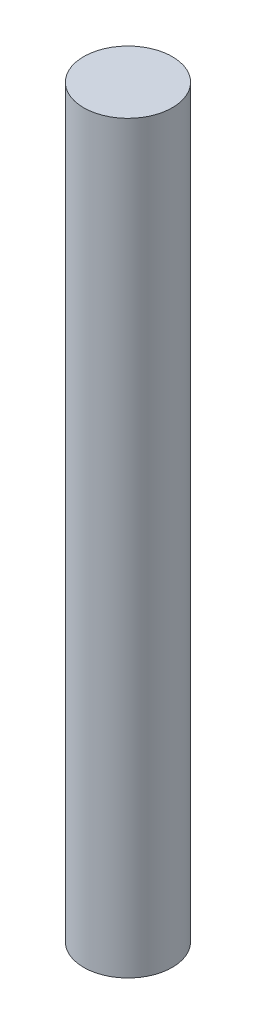
SolidWorks part; units mm, degrees
ref_plane "Front" through (0, 0, 0) normal (0, 0, 1) x (1, 0, 0)
ref_plane "Top" through (0, 0, 0) normal (0, 1, 0) x (1, 0, 0)
ref_plane "Right" through (0, 0, 0) normal (1, 0, 0) x (0, 0, -1)
sketch "Sketch1" plane through (0, 0, 0) normal (0, 1, 0) x (1, 0, 0)
  circle A0 centre (0, 0) radius 2.38
extrude "Boss-Extrude1" add sketch "Sketch1" along normal blind 40
